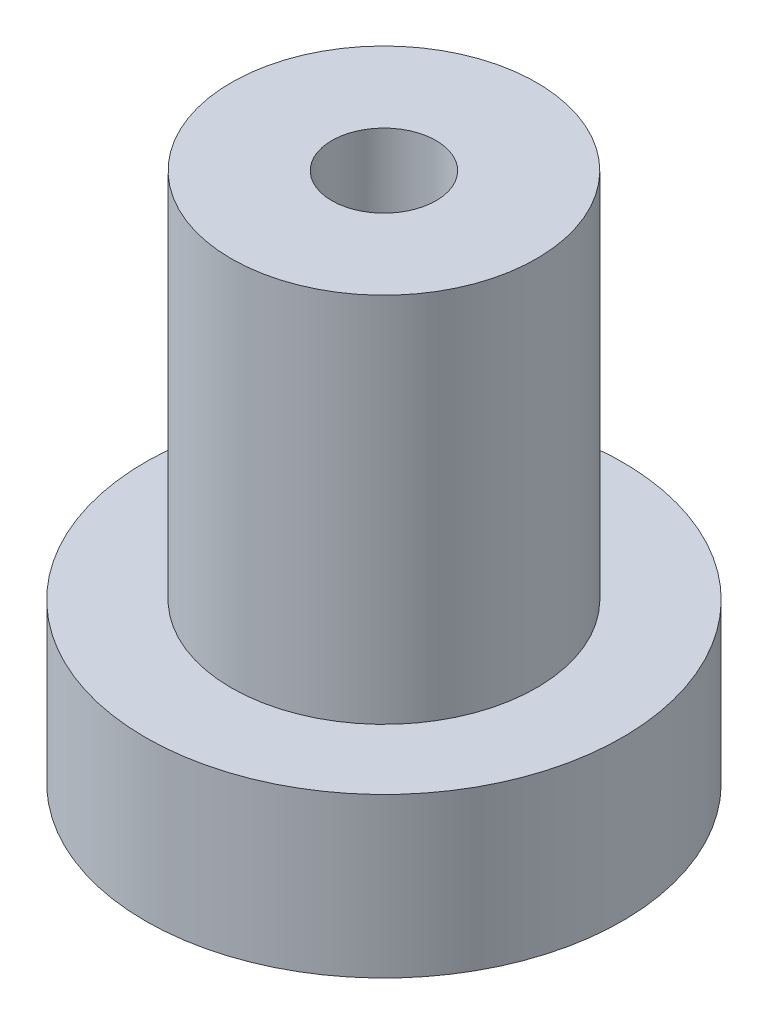
SolidWorks part; units mm, degrees
ref_plane "Front Plane" through (0, 0, 0) normal (0, 0, 1) x (1, 0, 0)
ref_plane "Top Plane" through (0, 0, 0) normal (0, 1, 0) x (1, 0, 0)
ref_plane "Right Plane" through (0, 0, 0) normal (1, 0, 0) x (0, 0, -1)
sketch "Sketch3" plane through (0, 0, 0) normal (0, 0, 1) x (1, 0, 0)
  line L0 (0, 0) -> (9.525, 0)
  line L1 (9.525, 0) -> (9.525, 6.35)
  line L2 (9.525, 6.35) -> (6.096, 6.35)
  line L3 (6.096, 6.35) -> (6.096, 21.193)
  line L6 (6.096, 21.193) -> (0, 21.193)
  line L7 (0, 21.193) -> (0, 0)
  line L8 (0, 10.5965) -> (12.7, 10.5965) construction
  dimension "D1" = 6.096
  dimension "D2" = 14.843
  dimension "D3" = 9.525
  dimension "D4" = 6.35
revolve "Revolve1" add sketch "Sketch3" angle 360 about L7
hole_wizard "#8-32 Tapped Hole1" positions "Sketch5" profile "Sketch4" tap size "#8-32" standard "ANSI Inch" end condition through all
sketch "Sketch5" plane through (0, 21.193, 0) normal (0, 1, 0) x (1, 0, 0)
  point P0 (0, 0)
sketch "Sketch4" plane through (0, 21.193, 0) normal (1, 0, 0) x (0, 0, 1)
  line L0 (0, 0) -> (0, 21.193)
  line L1 (0, 21.193) -> (2.0828, 21.193)
  line L2 (2.0828, 21.193) -> (2.0828, 0)
  line L5 (2.0828, 0) -> (0, 0)
  line L11 (0, -6.35) -> (0, 107.95) construction
  dimension "Thread Major Dia." = 4.1656
  dimension "Thru Tap Drill Depth" = 21.193
sketch "Sketch6" plane through (0, 0, 0) normal (0, -1, 0) x (1, 0, 0)
  line L1 (2.3699, 4.5527) -> (-2.7578, 4.3288)
  line L2 (-2.7578, 4.3288) -> (-5.1278, -0.224)
  line L3 (-5.1278, -0.224) -> (-2.3699, -4.5527)
  line L4 (-2.3699, -4.5527) -> (2.7578, -4.3288)
  line L5 (2.7578, -4.3288) -> (5.1278, 0.224)
  line L6 (5.1278, 0.224) -> (2.3699, 4.5527)
  circle A0 centre (0, 0) radius 4.445 construction
  dimension "D1" = 8.89
extrude "Cut-Extrude1" cut sketch "Sketch6" against normal blind 3.556
